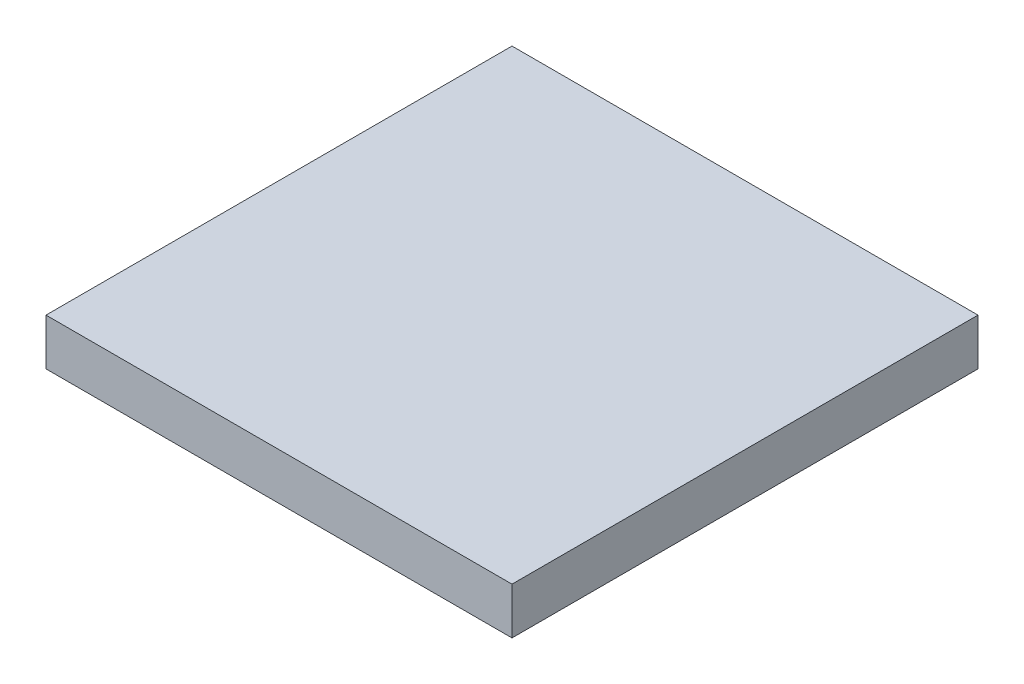
SolidWorks part; units mm, degrees
ref_plane "Plan de face" through (0, 0, 0) normal (0, 0, 1) x (1, 0, 0)
ref_plane "Plan de dessus" through (0, 0, 0) normal (0, 1, 0) x (1, 0, 0)
ref_plane "Plan de droite" through (0, 0, 0) normal (1, 0, 0) x (0, 0, -1)
sketch "Esquisse1" plane through (0, 0, 0) normal (0, 1, 0) x (1, 0, 0)
  line L1 (-150, -150) -> (150, -150)
  line L2 (-150, -150) -> (-150, 150)
  line L3 (-150, 150) -> (150, 150)
  line L4 (150, -150) -> (150, 150)
  line L5 (-150, -150) -> (150, 150) construction
  line L6 (-150, 150) -> (150, -150) construction
  point P0 (0, 0)
  dimension "D1" = 300
  dimension "D2" = 300
extrude "Boss.-Extru.1" add sketch "Esquisse1" along normal blind 30
